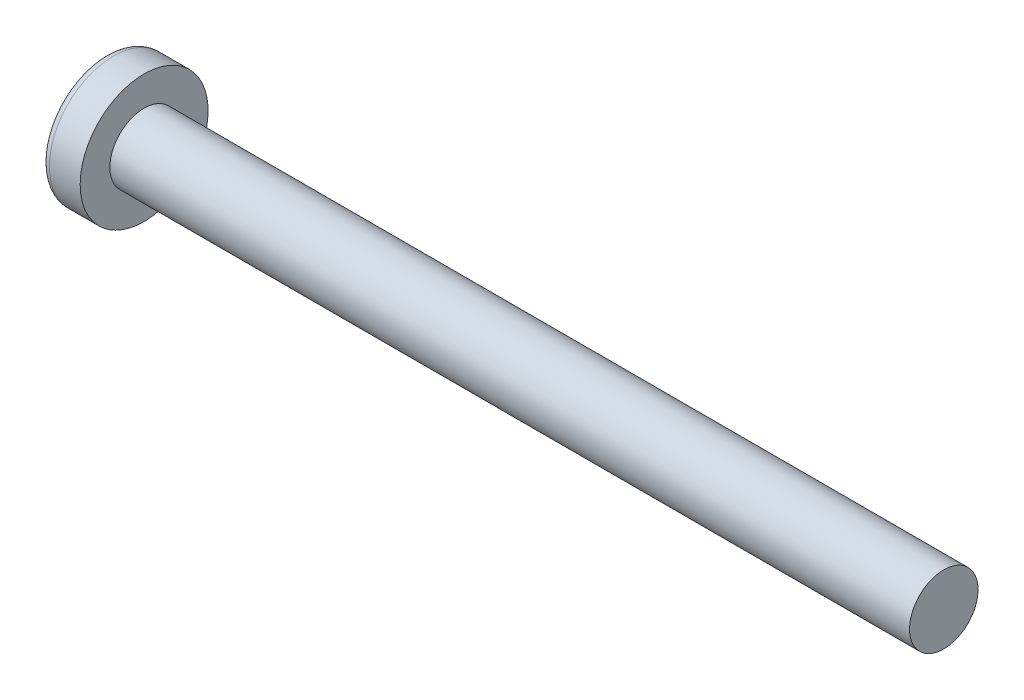
SolidWorks part; units mm, degrees
ref_plane "Plane1" through (0, 0, 0) normal (0, 0, 1) x (1, 0, 0)
ref_plane "Plane2" through (0, 0, 0) normal (0, 1, 0) x (1, 0, 0)
ref_plane "Plane3" through (0, 0, 0) normal (1, 0, 0) x (0, 0, -1)
sketch "BodySke" plane through (0, 0, 0) normal (0, 0, 1) x (1, 0, 0)
  line L0 (2.4, 1.5) -> (2.4, 2.8)
  line L1 (2.9, 6.35) -> (2.9, -3.175) construction
  line L2 (-25.4, 0) -> (127, 0) construction
  line L3 (37.4, 0) -> (0, 0)
  line L4 (2.4, 1.5) -> (37.4, 1.5)
  line L5 (37.4, 1.5) -> (37.4, 0)
  line L6 (1.0534, 2.8) -> (2.4, 2.8)
  line L7 (2.4, -1.5) -> (37.4, -1.5) construction
  line L8 (7.4, 6.35) -> (7.4, -3.175) construction
  arc A0 (0.7472, 2.6293) -> (0, 0) centre (5, 0) ccw
  arc A2 (0.7472, 2.6293) -> (1.0534, 2.8) centre (1.0534, 2.44) cw
  dimension "Head_fillet_rad" = 0.36
  dimension "Head_crown_rad" = 5
  dimension "Head_ht" = 2.4
  dimension "Diameter" = 3
  dimension "Length" = 35
  dimension "Head_dia" = 5.6
  dimension "Advance" = 0.5
  dimension "Thread_nom" = 30
revolve "Base-Revolve" add sketch "BodySke" angle 360 about L2
cosmetic thread "ThreadCosmetic" [suppressed] parameters "Thread_length"=30, "Thread_minor"=2.439
sketch "Sketch3" plane through (0, 0, 0) normal (1, 0, 0) x (0, 0, -1)
  line L0 (0.37, -1.45) -> (-0.37, -1.45)
  line L1 (0.37, -1.45) -> (0.37, 1.45)
  line L2 (-0.37, 1.45) -> (0.37, 1.45)
  line L3 (-0.37, 1.45) -> (-0.37, -1.45)
  dimension "D1" = 1.45
  dimension "Cross_dia" = 2.9
  dimension "D2" = 0.37
  dimension "Cross_width" = 0.74
ref_plane "Plane4" through (1.76, 0, 0) normal (1, 0, 0) x (0, 0, -1)
sketch "Sketch4" plane through (1.76, 0, 0) normal (1, 0, 0) x (0, 0, -1)
  line L0 (0.185, -0.185) -> (-0.185, -0.185)
  line L1 (0.185, -0.185) -> (0.185, 0.185)
  line L2 (-0.185, 0.185) -> (0.185, 0.185)
  line L3 (-0.185, 0.185) -> (-0.185, -0.185)
  dimension "D1" = 0.37
  dimension "D2" = 0.37
  dimension "D3" = 0.185
  dimension "D4" = 0.185
loft "Cut-Loft1" cut profiles "Sketch3", "Sketch4"
pattern_circular "CirPattern1" count 2 every 90 about axis through (-25.4, 0, 0) along (1, 0, 0)
sketch "ThdSchSke" plane through (0, 0, 0) normal (0, 0, 1) x (1, 0, 0)
  line L0 (7.4, -1.2195) -> (7.2036, -1.5)
  line L1 (7.4, -1.2195) -> (7.5964, -1.5)
  line L2 (7.5964, -1.5) -> (7.5964, -1.875)
  line L3 (-3.175, 0) -> (5.1513, 0) construction
  line L5 (7.5964, -1.875) -> (7.2036, -1.875)
  line L6 (7.2036, -1.875) -> (7.2036, -1.5)
  dimension "Thread_minor" = 2.439
  dimension "Diameter" = 3
  dimension "Start" = 7.4
  dimension "SideAngle" = 55
  dimension "VeeAngle" = 70
  dimension "Overcut" = 3.75
revolve "ThreadSchematic" [suppressed] cut sketch "ThdSchSke" angle 360 about L3
pattern_linear "ThdSchPat" [suppressed]
equation "\"D1@Sketch3\" = \"Cross_dia@Sketch3\" / 2"
equation "\"D2@Sketch3\" = \"Cross_width@Sketch3\" / 2"
equation "\"D1@Sketch4\" = \"Cross_width@Sketch3\" *.5"
equation "\"D2@Sketch4\" = \"D1@Sketch4\""
equation "\"D3@Sketch4\" = \"D1@Sketch4\" / 2"
equation "\"D4@Sketch4\" = \"D2@Sketch4\" / 2"
equation "\"Thread_length@ThreadCosmetic\" = ((sgn( (\"Length@BodySke\" - \"Advance@BodySke\" ) - \"Thread_nom@BodySke\" )-1)*( (\"Length@BodySke\" - \"Advance@BodySke\" ) - \"Thread_nom@BodySke\" ))/-2+ \"Thread_nom@BodySke\""
equation "\"Thread_minor@ThdSchSke\" = \"Thread_minor@ThreadCosmetic\""
equation "\"Diameter@ThdSchSke\" = \"Diameter@BodySke\""
equation "\"Overcut@ThdSchSke\" = \"Diameter@BodySke\" * 1.25"
equation "\"Start@ThdSchSke\" = \"Head_ht@BodySke\" + \"Length@BodySke\" - \"Thread_length@ThreadCosmetic\"  '---Non-countersunk---"
equation "\"Num_threads@ThdSchPat\" = int( \"Thread_length@ThreadCosmetic\" / \"Advance@BodySke\" + 0.999 )  + 1"
equation "\"Advance@ThdSchPat\" = \"Thread_length@ThreadCosmetic\" /  (\"Num_threads@ThdSchPat\" - 1) 'relax it"
